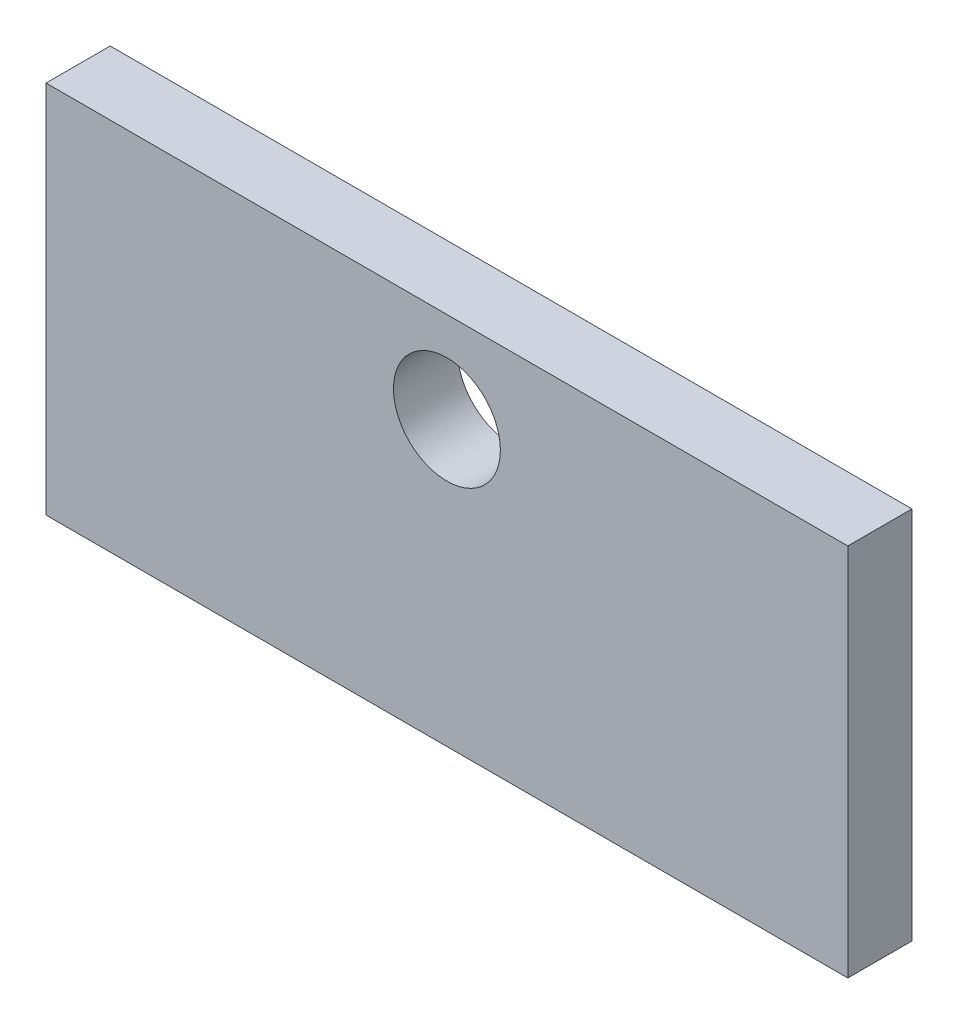
SolidWorks part; units mm, degrees
ref_plane "Alzado" through (0, 0, 0) normal (0, 0, 1) x (1, 0, 0)
ref_plane "Planta" through (0, 0, 0) normal (0, 1, 0) x (1, 0, 0)
ref_plane "Vista lateral" through (0, 0, 0) normal (1, 0, 0) x (0, 0, -1)
sketch "Croquis1" plane through (0, 0, 0) normal (0, 0, 1) x (1, 0, 0)
  line L0 (0, 0) -> (0, 70)
  line L1 (0, 70) -> (150, 70)
  line L2 (150, 70) -> (150, 0)
  line L3 (150, 0) -> (0, 0)
  dimension "D1" = 70
  dimension "D2" = 150
extrude "Saliente-Extruir1" add sketch "Croquis1" along normal blind 12
sketch "Croquis3" plane through (0, 0, 12) normal (0, 0, 1) x (1, 0, 0)
  line L2 (75, 53) -> (0, 53) construction
  line L3 (0, 70) -> (0, 0) construction
  circle A0 centre (75, 53) radius 10
  point P0 (0, 0)
  point P8 (67.5, 70)
  dimension "D1" = 75
extrude "Cortar-Extruir1" cut sketch "Croquis3" against normal through all
